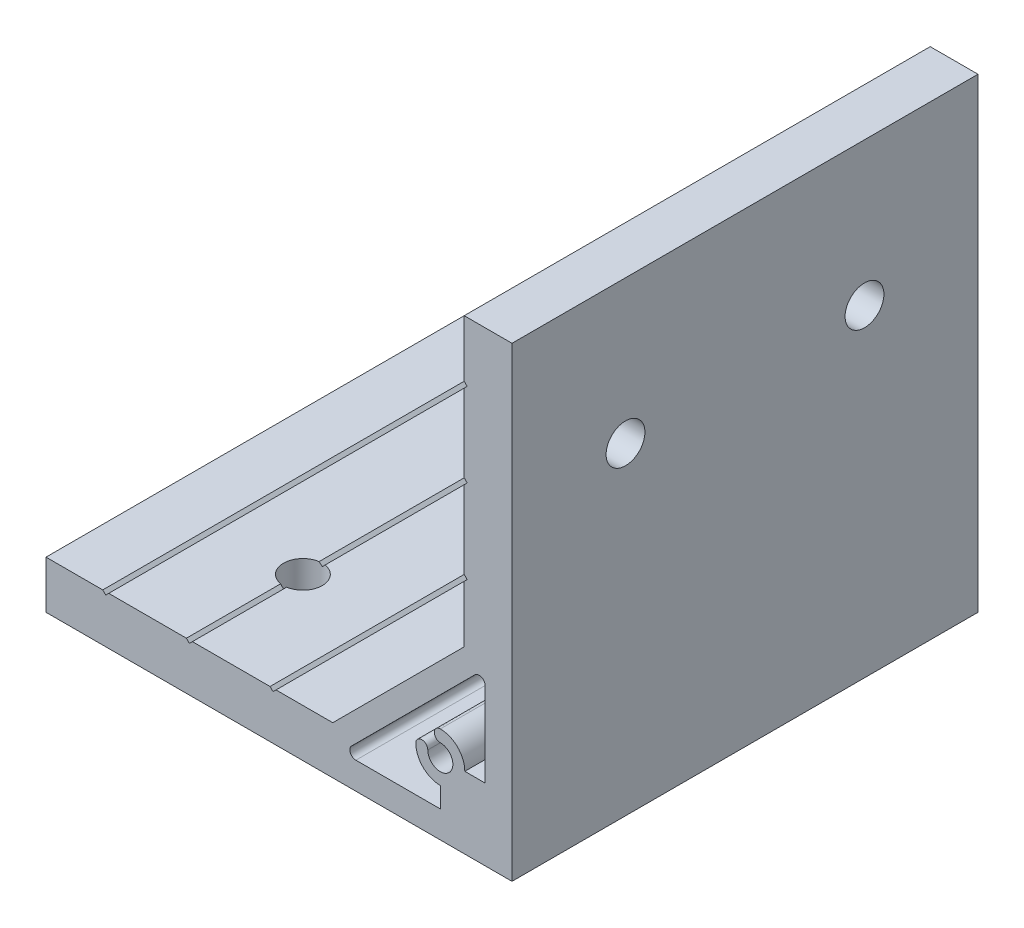
SolidWorks part; units mm, degrees
material "6063 T5"
ref_plane "Спереди" through (0, 0, 0) normal (0, 0, 1) x (1, 0, 0)
ref_plane "Сверху" through (0, 0, 0) normal (0, 1, 0) x (1, 0, 0)
ref_plane "Справа" through (0, 0, 0) normal (1, 0, 0) x (0, 0, -1)
sketch "Эскиз1" plane through (0, 0, 0) normal (0, 0, 1) x (1, 0, 0)
  line L0 (-78, 0) -> (0, 0)
  line L1 (0, 0) -> (0, 78)
  line L3 (-8, 53.5) -> (-8, 40.5)
  line L4 (-8, 40.5) -> (-7.5, 40)
  line L5 (-7.5, 40) -> (-8, 39.5)
  line L6 (-8, 39.5) -> (-8, 30)
  line L7 (-8, 30) -> (-30, 8)
  line L8 (-30, 8) -> (-39.5, 8)
  line L9 (-39.5, 8) -> (-40, 7.5)
  line L10 (-40, 7.5) -> (-40.5, 8)
  line L11 (-40.5, 8) -> (-53.5, 8)
  line L13 (-4.5, 12) -> (-4.5, 26.136)
  line L14 (-6.2071, 26.8431) -> (-26.8431, 6.2071)
  line L15 (-26.136, 4.5) -> (-12, 4.5)
  line L16 (-12, 4.5) -> (-12, 7.9)
  line L17 (-7.9, 12) -> (-4.5, 12)
  line L18 (-8, 53.5) -> (-7.5, 54)
  line L19 (-7.5, 54) -> (-8, 54.5)
  line L20 (-8, 54.5) -> (-8, 67.5)
  line L21 (-8, 67.5) -> (-7.5, 68)
  line L22 (-7.5, 68) -> (-8, 68.5)
  line L23 (-8, 68.5) -> (-8, 78)
  line L24 (-8, 78) -> (0, 78)
  line L25 (-53.5, 8) -> (-54, 7.5)
  line L26 (-54, 7.5) -> (-54.5, 8)
  line L27 (-54.5, 8) -> (-67.5, 8)
  line L28 (-67.5, 8) -> (-68, 7.5)
  line L29 (-68, 7.5) -> (-68.5, 8)
  line L30 (-68.5, 8) -> (-78, 8)
  line L31 (-78, 8) -> (-78, 0)
  arc A0 (-4.5, 26.136) -> (-6.2071, 26.8431) centre (-5.5, 26.136) ccw
  arc A1 (-26.8431, 6.2071) -> (-26.136, 4.5) centre (-26.136, 5.5) ccw
  arc A2 (-12, 7.9) -> (-16.1, 12) centre (-12, 12) cw
  arc A3 (-16.1, 12) -> (-14.1, 12) centre (-15.1, 12) cw
  arc A4 (-14.1, 12) -> (-12, 14.1) centre (-12, 12) ccw
  arc A5 (-12, 14.1) -> (-12, 16.1) centre (-12, 15.1) cw
  arc A6 (-12, 16.1) -> (-7.9, 12) centre (-12, 12) cw
  dimension "D6" = 4.2
  dimension "D7" = 1
  dimension "D9" = 1
  dimension "D2" = 8
  dimension "D3" = 135
  dimension "D4" = 12
  dimension "D5" = 12
  dimension "D8" = 30
  dimension "D10" = 3.5
  dimension "D11" = 4.5
  dimension "D12" = 40
  dimension "D13" = 1
  dimension "D14" = 54
  dimension "D15" = 68
  dimension "D16" = 78
extrude "Бобышка-Вытянуть1" add sketch "Эскиз1" along normal mid plane 78
sketch "Эскиз2" plane through (-8, 0, 0) normal (-1, 0, 0) x (0, 0, 1)
  line L1 (39, 54) -> (-39, 54) construction
  line L2 (-20, 54) -> (20, 54) construction
  circle A0 centre (-20, 54) radius 3.25
  circle A1 centre (20, 54) radius 3.25
  point P2 (0, 54)
  dimension "D1" = 6.5
  dimension "D2" = 40
extrude "Вырез-Вытянуть1" cut sketch "Эскиз2" against normal through all
sketch "Эскиз3" plane through (0, 8, 0) normal (0, 1, 0) x (1, 0, 0)
  line L1 (-54, -39) -> (-54, 39) construction
  line L2 (-54, 20) -> (-54, -20) construction
  circle A0 centre (-54, -20) radius 3.25
  circle A1 centre (-54, 20) radius 3.25
  point P2 (-54, 0)
  dimension "D1" = 6.5
  dimension "D2" = 40
extrude "Вырез-Вытянуть2" cut sketch "Эскиз3" against normal through all
